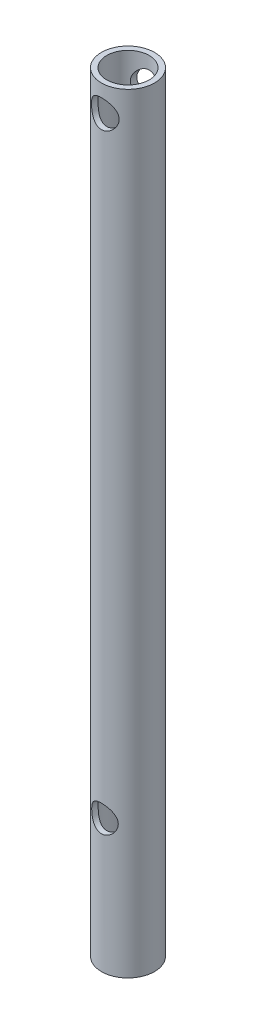
SolidWorks part; units mm, degrees
material "7075-T6 (SN)"
ref_plane "Płaszczyzna przednia" through (0, 0, 0) normal (0, 0, 1) x (1, 0, 0)
ref_plane "Płaszczyzna górna" through (0, 0, 0) normal (0, 1, 0) x (1, 0, 0)
ref_plane "Płaszczyzna prawa" through (0, 0, 0) normal (1, 0, 0) x (0, 0, -1)
sketch "Szkic1" plane through (0, 0, 0) normal (0, 1, 0) x (1, 0, 0)
  circle A0 centre (0, 0) radius 5
  circle A1 centre (0, 0) radius 4
  dimension "D1" = 1
  dimension "D2" = 8
extrude "Dodanie-wyciągnięcie1" add sketch "Szkic1" along normal blind 145
sketch "Szkic2" plane through (0, 0, 0) normal (0, 0, 1) x (1, 0, 0)
  line L0 (-5, 0) -> (5, 0) construction
  line L2 (-5, 145) -> (-5, 0) construction
  line L5 (5, 145) -> (-5, 145) construction
  circle A0 centre (0, 140) radius 2.6057
  circle A6 centre (0, 25) radius 2.5
  dimension "D3" = 5
  dimension "D5" = 5
  dimension "D2" = 5
  dimension "D7" = 25
extrude "Wytnij-wyciągnięcie1" cut sketch "Szkic2" against normal mid plane 30
